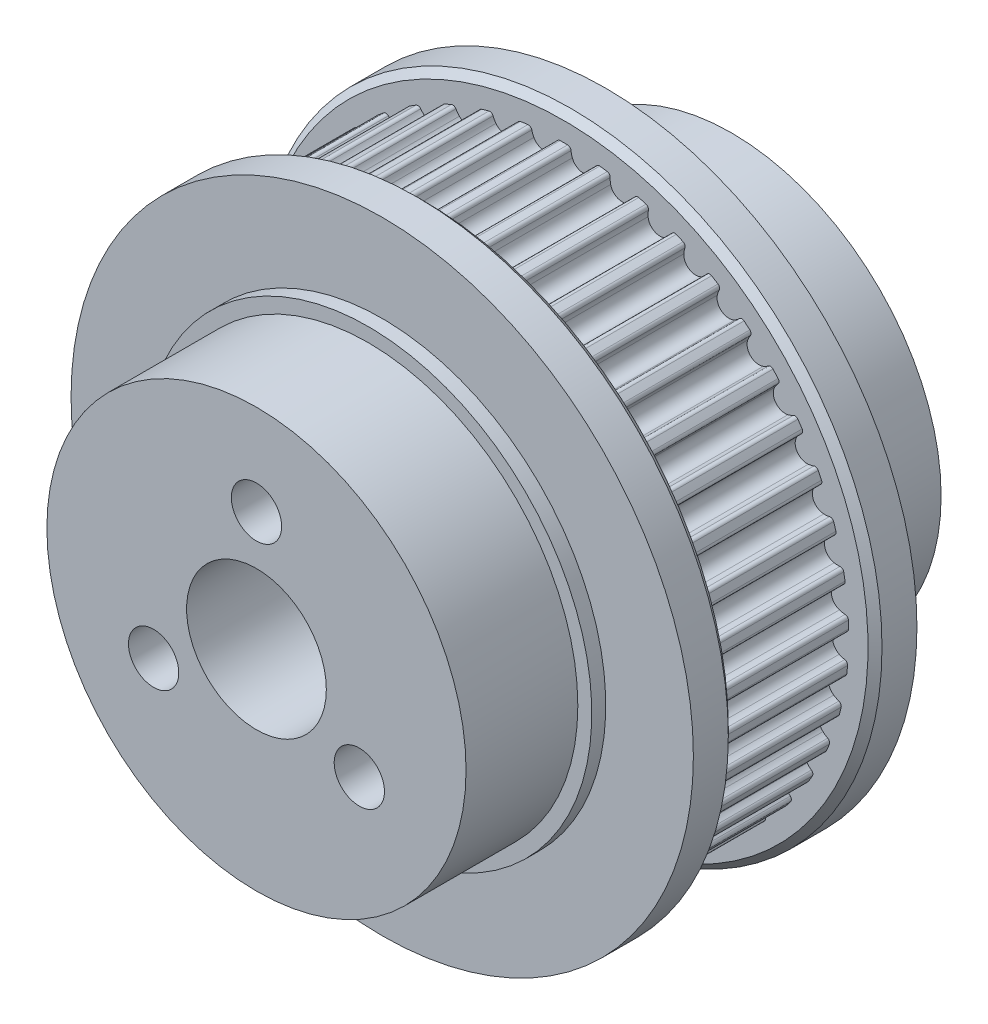
SolidWorks part; units mm, degrees
material "ABS"
ref_plane "正面" through (0, 0, 0) normal (0, 0, 1) x (1, 0, 0)
ref_plane "平面" through (0, 0, 0) normal (0, 1, 0) x (1, 0, 0)
ref_plane "右側面" through (0, 0, 0) normal (1, 0, 0) x (0, 0, -1)
sketch "ｽｹｯﾁ1" plane through (0, 0, 0) normal (0, 0, 1) x (1, 0, 0)
  circle A0 centre (0, 0) radius 20.7697
  dimension "D1" = 41.5394
extrude "ﾎﾞｽ - 押し出し1" add sketch "ｽｹｯﾁ1" along normal mid plane 10
sketch "ｽｹｯﾁ2" plane through (0, 0, 5) normal (0, 0, 1) x (1, 0, 0)
  line L0 (0, 20.3887) -> (0, 0) construction
  line L1 (0, 0) -> (1.402, 20.0498) construction
  line L2 (0, 20.7697) -> (0, 20.3887)
  line L3 (1.3427, 19.2018) -> (1.4488, 20.7191)
  arc A0 (0, 20.3887) -> (0.2693, 20.3869) centre (0, 0) cw
  arc A1 (0.5151, 20.1577) -> (0.6055, 19.753) centre (2.0299, 20.2837) ccw
  arc A2 (0.5151, 20.1577) -> (0.2693, 20.3869) centre (0.266, 20.137) ccw
  arc A3 (1.3427, 19.2018) -> (0.6055, 19.753) centre (1.402, 20.0498) cw
  circle A4 centre (0, 0) radius 20.7697 construction
  circle A5 centre (0, 0) radius 20.7697 construction
  circle A6 centre (0, 0) radius 19.2487 construction
  circle A7 centre (0, 0) radius 20.3887 construction
  arc A8 (0, 20.7697) -> (1.4488, 20.7191) centre (0, 0) cw
  circle M4 centre (0, 0) radius 20.7697
  dimension "D1" = 0.25
  dimension "D2" = 1.52
  dimension "D3" = 0.85
  dimension "D4" = 0.61
  dimension "D5" = 0.381
  dimension "D6" = 4
  dimension "D7" = 1.14
extrude "ｶｯﾄ - 押し出し1" cut sketch "ｽｹｯﾁ2" against normal through all contours A3 L3 L2 A0 A2 A1 M4
mirror "ﾐﾗｰ1" about plane through (0, 0, 0) normal (1, 0, 0) of "ｶｯﾄ - 押し出し1"
pattern_circular "円形ﾊﾟﾀｰﾝ1" count 45 over 360 about axis through (0, 0, 0) along (0, 0, 1) of "ﾐﾗｰ1", "ｶｯﾄ - 押し出し1"
sketch "ｽｹｯﾁ3" plane through (0, 0, 5) normal (0, 0, 1) x (1, 0, 0)
  circle A0 centre (0, 0) radius 22.2697
  dimension "D1" = 44.5394
extrude "ﾎﾞｽ - 押し出し2" add sketch "ｽｹｯﾁ3" along normal blind 3
chamfer "面取り1" distance 0.5 angle 45 1 edges at (22.2697, 0, 5)
sketch "ｽｹｯﾁ7" plane through (0, 0, -5) normal (0, 0, -1) x (-1, 0, 0)
  circle A0 centre (0, 0) radius 22.2697
  circle A1 centre (0, 0) radius 22.2697 construction
extrude "ﾎﾞｽ - 押し出し3" add sketch "ｽｹｯﾁ7" along normal blind 3 contours A0
chamfer "面取り2" distance 0.5 angle 45 1 edges at (-22.2697, 0, -5)
sketch "ｽｹｯﾁ12" plane through (0, 0, -8) normal (0, 0, -1) x (-1, 0, 0)
  circle A0 centre (0, 0) radius 15
  dimension "D1" = 30
extrude "ﾎﾞｽ - 押し出し4" add sketch "ｽｹｯﾁ12" along normal blind 9
sketch "ｽｹｯﾁ16" plane through (0, 0, -8) normal (0, 0, -1) x (-1, 0, 0)
  circle A0 centre (0, 0) radius 16
  circle A1 centre (0, 0) radius 15
  circle A2 centre (0, 0) radius 15 construction
  dimension "D1" = 1
extrude "ﾎﾞｽ - 押し出し7" add sketch "ｽｹｯﾁ16" along normal offset from surface (1 mm away) 8 up to face at (-15, 0, -17)
mirror "ﾐﾗｰ3" about plane through (0, 0, 0) normal (0, 0, 1) of "ﾎﾞｽ - 押し出し7", "ﾎﾞｽ - 押し出し4"
sketch "ｽｹｯﾁ4" plane through (0, 0, 0) normal (0, 0, 1) x (1, 0, 0)
  circle A0 centre (0, 0) radius 5
  dimension "D1" = 10
extrude "ｶｯﾄ - 押し出し4" cut sketch "ｽｹｯﾁ4" against normal through all both and the other way through all
hole_wizard "M3 穴付きねじ用座ぐり穴1" positions "ｽｹｯﾁ10" profile "ｽｹｯﾁ9" counterbore size "M3" standard "JIS" end condition through all
sketch "ｽｹｯﾁ10" plane through (0, 0, -17) normal (0, 0, -1) x (-1, 0, 0)
  point P0 (0, 8.5)
  dimension "D1" = 8.5
sketch "ｽｹｯﾁ9" plane through (0, 8.5, -17) normal (1, 0, 0) x (0, 1, 0)
  line L0 (0, 0) -> (0, 34)
  line L1 (0, 34) -> (1.8, 34)
  line L3 (1.8, 34) -> (1.8, 13)
  line L4 (1.8, 13) -> (3.25, 13)
  line L5 (3.25, 13) -> (3.25, 0)
  line L7 (3.25, 0) -> (0, 0)
  line L11 (0, -6.35) -> (0, 107.95) construction
  dimension "通し穴の直径" = 3.6
  dimension "通し穴の深さ" = 34
  dimension "座ぐり穴の直径" = 6.5
  dimension "座ぐり穴の深さ" = 13
pattern_circular "円形ﾊﾟﾀｰﾝ2" count 3 over 360 about axis through (0, 0, 0) along (0, 0, 1) of "M3 穴付きねじ用座ぐり穴1"
equation "\"n\"= 45"
equation "\"p\"= 2.9"
equation "\"pd\"= \"n\" * \"p\" / pi"
equation "\"D1@ｽｹｯﾁ1\"=\"pd\""
equation "\"width\"= 10"
equation "\"D1@ﾎﾞｽ - 押し出し1\"=\"width\""
equation "\"r1\"= 0.25mm"
equation "\"r2\"= 1.52"
equation "\"r3\"= 0.85"
equation "\"b\"= 0.61mm"
equation "\"h2\"= 1.14mm"
equation "\"h1\"= 2.4mm"
equation "\"i\"= 1.26mm"
equation "\"pld\"= 0.381mm"
equation "\"D1@ｽｹｯﾁ2\"=\"r1\""
equation "\"D2@ｽｹｯﾁ2\"=\"r2\""
equation "\"D3@ｽｹｯﾁ2\"=\"r3\""
equation "\"D4@ｽｹｯﾁ2\"=\"b\""
equation "\"D5@ｽｹｯﾁ2\"=\"pld\""
equation "\"angle\"= 180 / \"n\""
equation "\"D6@ｽｹｯﾁ2\"=\"angle\""
equation "\"D7@ｽｹｯﾁ2\"=\"h2\""
equation "\"D1@円形ﾊﾟﾀｰﾝ1\"=\"n\""
equation "\"D1@ｽｹｯﾁ3\"=\"pd\"+3"
